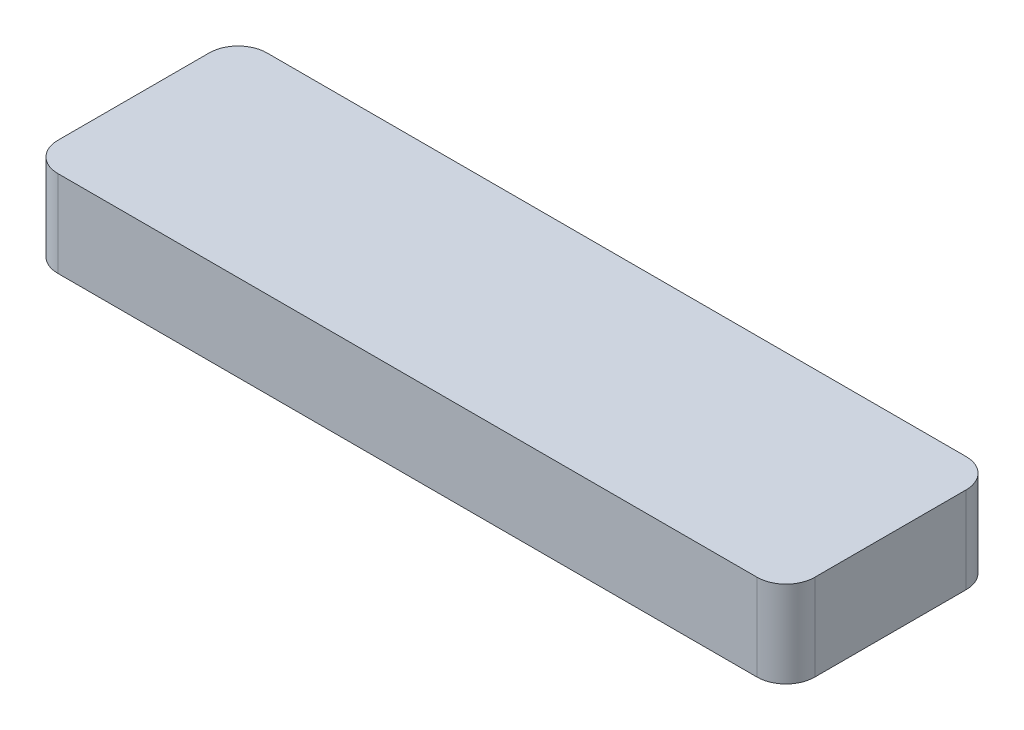
SolidWorks part; units mm, degrees
ref_plane "Plan de face" through (0, 0, 0) normal (0, 0, 1) x (1, 0, 0)
ref_plane "Plan de dessus" through (0, 0, 0) normal (0, 1, 0) x (1, 0, 0)
ref_plane "Plan de droite" through (0, 0, 0) normal (1, 0, 0) x (0, 0, -1)
sketch "Esquisse1" plane through (0, 0, 0) normal (0, 1, 0) x (1, 0, 0)
  line L0 (0, 0) -> (34.4602, 0) construction
  line L1 (0, 0) -> (0, 32.5563) construction
  line L3 (-24.25, -7.25) -> (24.25, -7.25)
  line L4 (-26.25, -5.25) -> (-26.25, 5.25)
  line L5 (-24.25, 7.25) -> (24.25, 7.25)
  line L6 (26.25, -5.25) -> (26.25, 5.25)
  arc A0 (-26.25, 5.25) -> (-24.25, 7.25) centre (-24.25, 5.25) cw
  arc A1 (-24.25, -7.25) -> (-26.25, -5.25) centre (-24.25, -5.25) cw
  arc A2 (26.25, -5.25) -> (24.25, -7.25) centre (24.25, -5.25) cw
  arc A3 (24.25, 7.25) -> (26.25, 5.25) centre (24.25, 5.25) cw
  dimension "D3" = 2
  dimension "D1" = 52.5
  dimension "D2" = 14.5
extrude "Extrusion1" add sketch "Esquisse1" along normal blind 6
sketch "Esquisse6" plane through (0, 0, 0) normal (0, 0, 1) x (1, 0, 0)
  line L0 (0, 0) -> (0, 14.7261) construction
  line L1 (-12, 0) -> (-12, -5)
  line L2 (-24.25, 0) -> (24.25, 0) construction
  line L3 (-12, -5) -> (-13.75, -5)
  line L4 (-13.75, -5) -> (-15, -3.5)
  line L5 (-15, -3.5) -> (-14.5, -3.5)
  line L6 (-14.5, -3.5) -> (-14.5, 0)
  line L7 (-14.5, 0) -> (-12, 0)
  line L8 (-12, 10.6716) -> (-12, -14.3705) construction
  line L15 (12, 10.6716) -> (12, -14.3705) construction
  dimension "D1" = 24
  dimension "D2" = 5
  dimension "D3" = 5
  dimension "D4" = 6
  dimension "D5" = 3.5
  dimension "D6" = 3.5
revolve "Révolution1" add sketch "Esquisse6" angle 360 about L8
mirror "Symétrie1" about plane through (0, 0, 0) normal (1, 0, 0) of "Révolution1"
sketch "Esquisse7" plane through (0, 0, 0) normal (0, -1, 0) x (1, 0, 0)
  line L0 (-19.3579, 0) -> (17.927, 0) construction
  line L2 (-15, 0.5) -> (15, 0.5)
  line L3 (-15, 0.5) -> (-15, -0.5)
  line L4 (-15, -0.5) -> (15, -0.5)
  line L5 (15, 0.5) -> (15, -0.5)
  circle A2 centre (-12, 0) radius 3 construction
  circle A3 centre (12, 0) radius 3 construction
  dimension "D1" = 1
extrude "Enlèv. mat.-Extru.1" cut sketch "Esquisse7" along normal through all
